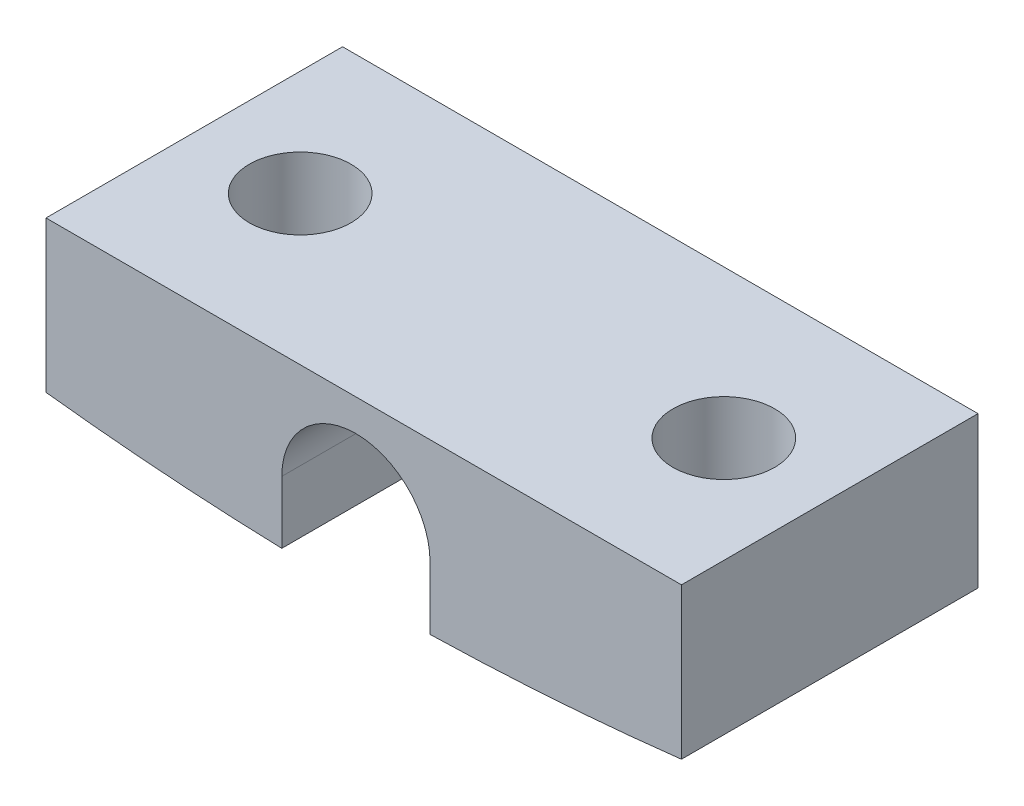
SolidWorks part; units mm, degrees
ref_plane "Front Plane" through (0, 0, 0) normal (0, 0, 1) x (1, 0, 0)
ref_plane "Top Plane" through (0, 0, 0) normal (0, 1, 0) x (1, 0, 0)
ref_plane "Right Plane" through (0, 0, 0) normal (1, 0, 0) x (0, 0, -1)
sketch "Sketch1" plane through (0, 0, 0) normal (0, 0, 1) x (1, 0, 0)
  line L0 (0, 0) -> (15, 0)
  line L1 (15, 0) -> (15, -3.5659)
  line L2 (0, 0) -> (0, -3.5659)
  line L3 (5.5659, -2.5) -> (5.5659, -3.9712)
  line L4 (9.0659, -2.5) -> (9.0659, -3.9811)
  arc A0 (15, -3.5659) -> (9.0659, -3.9811) centre (7.5, 61) cw
  arc A1 (9.0659, -2.5) -> (5.5659, -2.5) centre (7.3159, -2.5) ccw
  arc A2 (5.5659, -3.9712) -> (0, -3.5659) centre (7.5, 61) cw
  dimension "D2" = 65
  dimension "D3" = 61
  dimension "D4" = 2.5
  dimension "D5" = 3.5
  dimension "D1" = 15
extrude "Boss-Extrude1" add sketch "Sketch1" along normal blind 7
sketch "Sketch2" plane through (0, 0, 0) normal (0, 1, 0) x (1, 0, 0)
  line L0 (15, -3.5) -> (0, -3.5) construction
  line L1 (15, -7) -> (15, 0) construction
  line L2 (0, -7) -> (0, 0) construction
  line L3 (7.5, 0) -> (7.5, -7) construction
  line L4 (15, 0) -> (0, 0) construction
  line L5 (15, -7) -> (0, -7) construction
  circle A0 centre (12.5, -3.5) radius 1.2
  circle A1 centre (2.5, -3.5) radius 1.2
  dimension "D1" = 2.4
  dimension "D2" = 2.4
  dimension "D3" = 5
  dimension "D4" = 5
extrude "Cut-Extrude1" cut sketch "Sketch2" against normal blind 10
